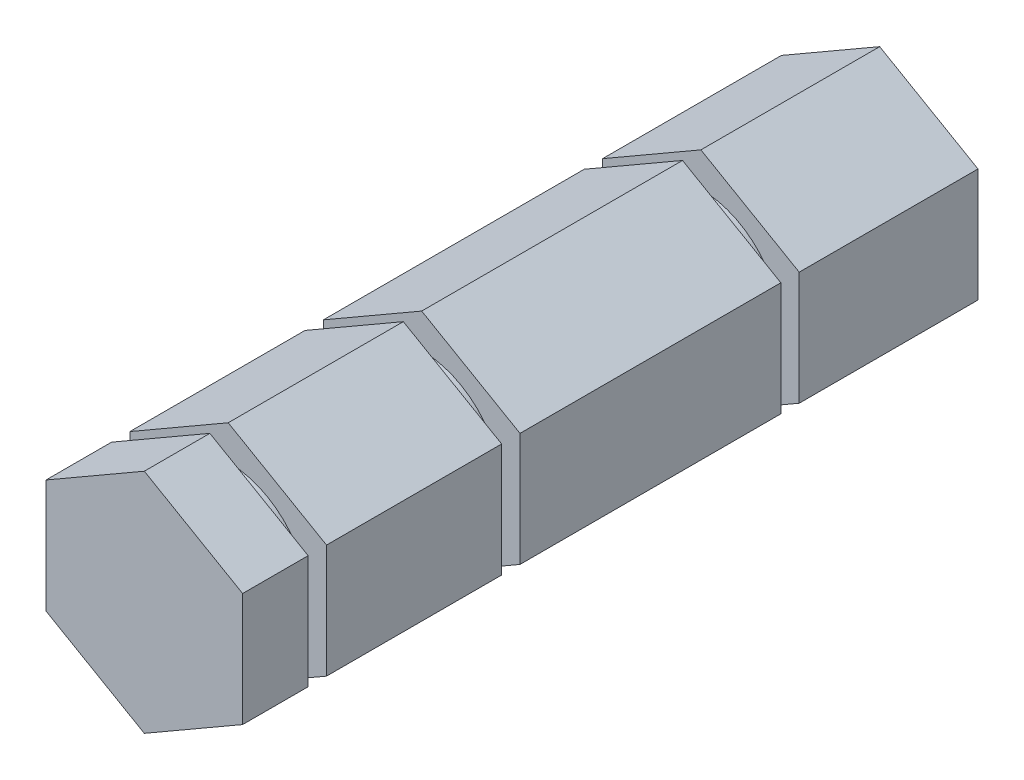
SolidWorks part; units mm, degrees
ref_plane "Front Plane" through (0, 0, 0) normal (0, 0, 1) x (1, 0, 0)
ref_plane "Top Plane" through (0, 0, 0) normal (0, 1, 0) x (1, 0, 0)
ref_plane "Right Plane" through (0, 0, 0) normal (1, 0, 0) x (0, 0, -1)
sketch "Sketch1" plane through (0, 0, 0) normal (0, 0, 1) x (1, 0, 0)
  line L1 (0, 5.4993) -> (-4.7625, 2.7496)
  line L2 (-4.7625, 2.7496) -> (-4.7625, -2.7496)
  line L3 (-4.7625, -2.7496) -> (0, -5.4993)
  line L4 (0, -5.4993) -> (4.7625, -2.7496)
  line L5 (4.7625, -2.7496) -> (4.7625, 2.7496)
  line L6 (4.7625, 2.7496) -> (0, 5.4993)
  circle A0 centre (0, 0) radius 4.7625 construction
  dimension "D1" = 9.525
extrude "Boss-Extrude1" add sketch "Sketch1" along normal blind 40.6146
ref_plane "Plane1" through (0, 0, 22.6314) normal (0, 0, -1) x (-1, 0, 0)
sketch "Sketch5" plane through (0, 0, 22.6314) normal (0, 0, -1) x (-1, 0, 0)
  line L1 (-5.93, -6.1669) -> (5.1735, -6.1669)
  line L2 (-5.93, -6.1669) -> (-5.93, 5.9781)
  line L3 (-5.93, 5.9781) -> (5.1735, 5.9781)
  line L4 (5.1735, -6.1669) -> (5.1735, 5.9781)
  circle A0 centre (0, 0) radius 3.8481
  dimension "D1" = 7.6962
extrude "Cut-Extrude2" cut sketch "Sketch5" against normal mid plane 0.889
ref_plane "Plane6" through (0, 0, 32.004) normal (0, 0, -1) x (-1, 0, 0)
sketch "Sketch10" plane through (0, 0, 32.004) normal (0, 0, -1) x (-1, 0, 0)
  line L1 (-6.0829, 5.6436) -> (5.9197, 5.6436)
  line L2 (-6.0829, 5.6436) -> (-6.0829, -6.1505)
  line L3 (-6.0829, -6.1505) -> (5.9197, -6.1505)
  line L4 (5.9197, 5.6436) -> (5.9197, -6.1505)
  circle A0 centre (0, 0) radius 3.8481
  dimension "D1" = 7.6962
extrude "Cut-Extrude7" cut sketch "Sketch10" against normal mid plane 0.889
ref_plane "Plane5" through (0, 0, 9.1059) normal (0, 0, 1) x (1, 0, 0)
sketch "Sketch9" plane through (0, 0, 9.1059) normal (0, 0, 1) x (1, 0, 0)
  line L1 (-5.5529, 6.1325) -> (5.8139, 6.1325)
  line L2 (-5.5529, 6.1325) -> (-5.5529, -5.8155)
  line L3 (-5.5529, -5.8155) -> (5.8139, -5.8155)
  line L4 (5.8139, 6.1325) -> (5.8139, -5.8155)
  circle A0 centre (0, 0) radius 3.8481
  dimension "D1" = 7.6962
extrude "Cut-Extrude6" cut sketch "Sketch9" against normal mid plane 0.889
sketch "Sketch11" plane through (0, 0, 40.6146) normal (0, 0, 1) x (1, 0, 0)
  circle A0 centre (0, 0) radius 5.7451
extrude "Cut-Extrude8" cut sketch "Sketch11" against normal offset from surface (4.9911 mm away) 3.175 up to face at (-3.8481, 0, 32.4485)
